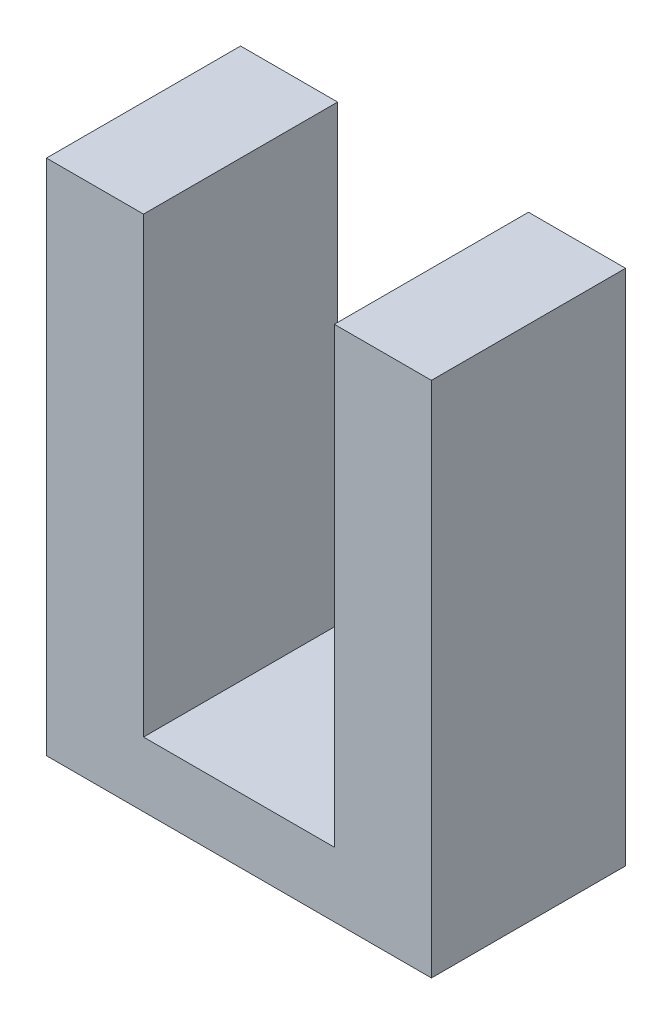
SolidWorks part; units mm, degrees
ref_plane "Alzado" through (0, 0, 0) normal (0, 0, 1) x (1, 0, 0)
ref_plane "Planta" through (0, 0, 0) normal (0, 1, 0) x (1, 0, 0)
ref_plane "Vista lateral" through (0, 0, 0) normal (1, 0, 0) x (0, 0, -1)
sketch "Croquis2" plane through (0, 0, 0) normal (0, 0, 1) x (1, 0, 0)
  line L0 (-2.975, 7) -> (-2.975, -1)
  line L1 (-2.975, -1) -> (2.975, -1)
  line L2 (2.975, -1) -> (2.975, 7)
  line L3 (2.975, 7) -> (1.475, 7)
  line L4 (1.475, 7) -> (1.475, 0)
  line L5 (1.475, 0) -> (-1.475, 0)
  line L6 (-1.475, 0) -> (-1.475, 7)
  line L7 (-1.475, 7) -> (-2.975, 7)
  point P2 (0, 0)
  point P10 (0, 0)
  dimension "D1" = 2.95
  dimension "D2" = 1.5
  dimension "D3" = 8
  dimension "D4" = 1
extrude "Saliente-Extruir1" add sketch "Croquis2" along normal mid plane 3
